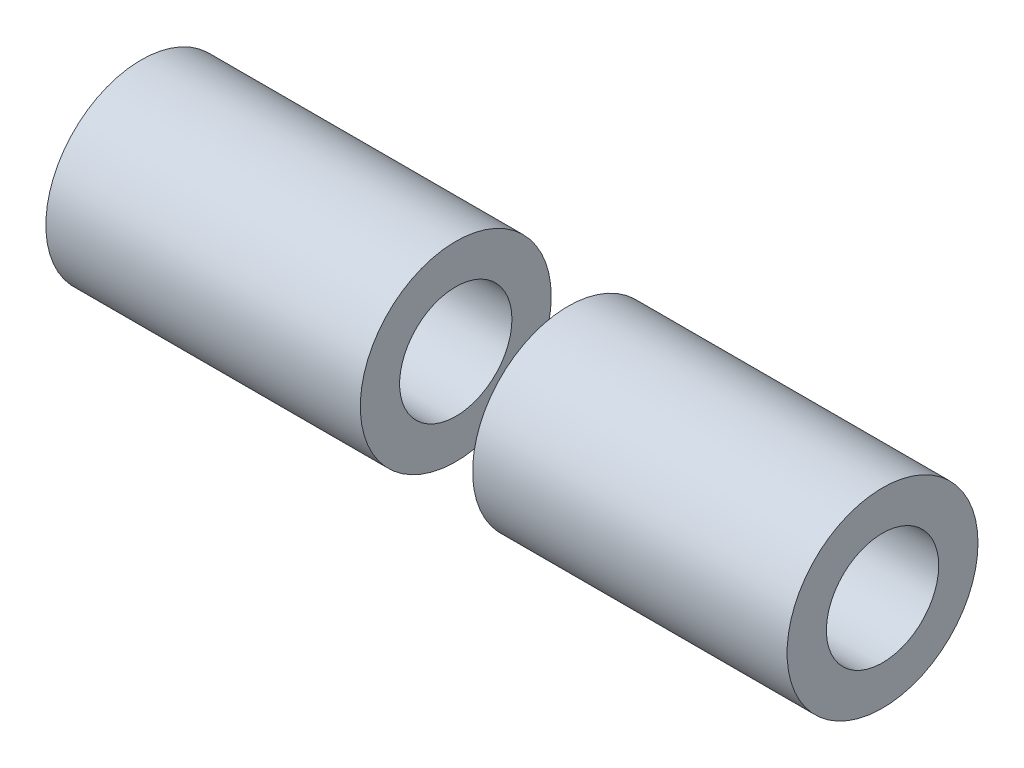
SolidWorks part; units mm, degrees
material "Silicon"
ref_plane "Front Plane" through (0, 0, 0) normal (0, 0, 1) x (1, 0, 0)
ref_plane "Top Plane" through (0, 0, 0) normal (0, 1, 0) x (1, 0, 0)
ref_plane "Right Plane" through (0, 0, 0) normal (1, 0, 0) x (0, 0, -1)
sketch "Sketch1" plane through (0, 0, 0) normal (1, 0, 0) x (0, 0, -1)
  circle A0 centre (0, 0) radius 5
  circle A1 centre (0, 0) radius 8.5
  dimension "D1" = 17
  dimension "D2" = 10
extrude "Boss-Extrude1" add sketch "Sketch1" along normal blind 28 from offset 5
mirror "Mirror2" about plane through (0, 0, 0) normal (1, 0, 0) of bodies 101
